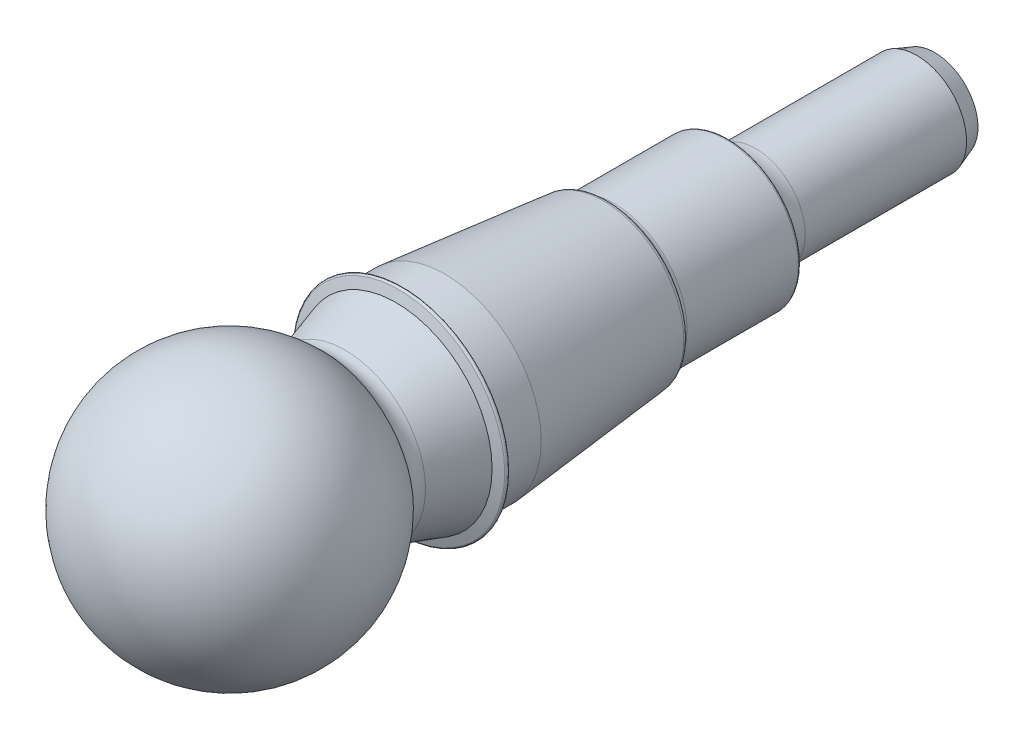
SolidWorks part; units mm, degrees
ref_plane "Vorne" through (0, 0, 0) normal (0, 0, 1) x (1, 0, 0)
ref_plane "Oben" through (0, 0, 0) normal (0, 1, 0) x (1, 0, 0)
ref_plane "Rechts" through (0, 0, 0) normal (1, 0, 0) x (0, 0, -1)
sketch "Skizze1" plane through (0, 0, 0) normal (1, 0, 0) x (0, 0, -1)
  line L0 (26, 0) -> (26, 10.3651) construction
  line L1 (23.6505, 10.6) -> (19.3, 10.6)
  line L2 (23.5, 20.3941) -> (23.5, -22.2368) construction
  line L3 (23.5, 33.5926) -> (23.5, -31.0123) construction
  line L15 (77.5, 4.75) -> (75.5218, 5.47)
  line L16 (75.5218, 5.47) -> (57.8, 5.47)
  line L17 (-20.2836, 0) -> (79.7863, 0) construction
  line L19 (77.5, 0) -> (77.5, 4.75)
  line L24 (77.5, 0) -> (-14.2875, 0)
  line L25 (54.5, 8) -> (42.2771, 8)
  line L28 (41.6276, 8.375) -> (41.5196, 8.5621)
  line L29 (41.0597, 8.8591) -> (23.6505, 10.6)
  line L32 (19.3, 10.6) -> (19.0334, 11.595)
  line L33 (18.632, 11.6038) -> (18.3, 10.5507)
  line L35 (18.3, 10.5507) -> (12.6959, 8.8374)
  line L39 (54.8, 7.7) -> (54.8, 7.47)
  arc A0 (54.8, 7.47) -> (54.9135, 6.9249) centre (56.166, 7.47) ccw
  arc A1 (54.9135, 6.9249) -> (55.2935, 6.3711) centre (56.5367, 7.6314) ccw
  arc A2 (55.2935, 6.3711) -> (56.1907, 5.7821) centre (57.2119, 8.3158) ccw
  arc A3 (56.1907, 5.7821) -> (57.8, 5.47) centre (57.8, 9.7748) ccw
  arc A4 (18.632, 11.6038) -> (19.0334, 11.595) centre (18.8314, 11.5409) cw
  arc A5 (9.4112, 10.75) -> (10.9744, 9.1485) centre (0, 0) cw construction
  arc A13 (54.8, 7.7) -> (54.5, 8) centre (54.5, 7.7) ccw
  arc A14 (41.6276, 8.375) -> (42.2771, 8) centre (42.2771, 8.75) ccw
  arc A17 (41.5196, 8.5621) -> (41.0597, 8.8591) centre (41, 8.2621) ccw
  arc A23 (10.3, 9.9016) -> (-14.2875, 0) centre (0, 0) ccw
  arc A24 (10.3, 9.9016) -> (12.6959, 8.8374) centre (12.1112, 10.75) ccw
  ellipse E0 centre (57.8, 7.47) end of major axis (54.8, 7.47) minor radius 2 construction
  dimension "D1" = 28.575
  dimension "D2" = 0.75
  dimension "D3" = 0.6
  dimension "D10" = 3
  dimension "D14" = 4.3048
  dimension "D15" = 2.7318
  dimension "D16" = 1.7703
  dimension "D17" = 1.366
  dimension "D21" = 0.3
  dimension "D25" = 42.2771
  dimension "D26" = 4.2
  dimension "D28" = 3
  dimension "D29" = 21.2
  dimension "D31" = 18.3
  dimension "D33" = 2
  dimension "D35" = 17.5
  dimension "D37" = 23.5
  dimension "D39" = 23.5
  dimension "D40" = 26
  dimension "D4" = 9.5
  dimension "D5" = 41
  dimension "D6" = 10.94
  dimension "D7" = 77.5
  dimension "D8" = 20
  dimension "D9" = 1.9782
  dimension "D12" = 54.8
  dimension "D19" = 14.94
  dimension "D22" = 16
  dimension "D23" = 60
  dimension "D24" = 5.711
  dimension "D27" = 75
  dimension "D30" = 23.6505
  dimension "D32" = 10.3
  dimension "D34" = 17
  dimension "D36" = 17.5
  dimension "D38" = 23.5
  dimension "D41" = 20.7301
revolve "Rotation1" add sketch "Skizze1" angle 360 about L17
